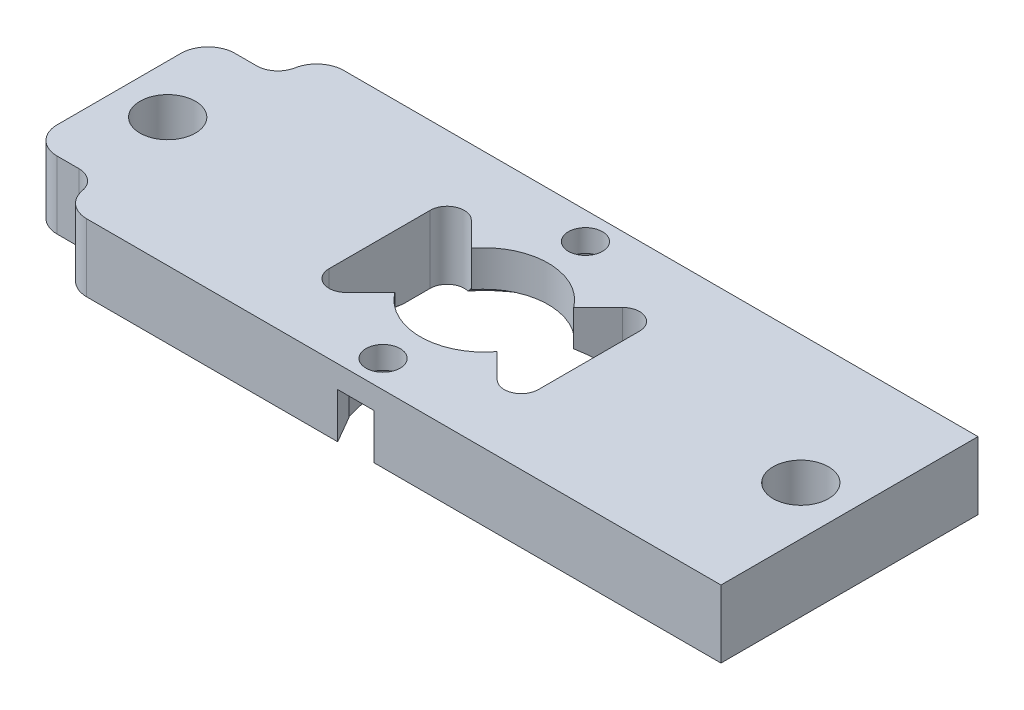
SolidWorks part; units mm, degrees
ref_plane "Front Plane" through (0, 0, 0) normal (0, 0, 1) x (1, 0, 0)
ref_plane "Top Plane" through (0, 0, 0) normal (0, 1, 0) x (1, 0, 0)
ref_plane "Right Plane" through (0, 0, 0) normal (1, 0, 0) x (0, 0, -1)
sketch "Sketch2" plane through (0, 0, 0) normal (0, 1, 0) x (1, 0, 0)
  line L1 (0, 0) -> (68.58, 0)
  line L2 (0, 0) -> (0, 24.13)
  line L3 (0, 24.13) -> (68.58, 24.13)
  line L4 (68.58, 0) -> (68.58, 24.13)
  circle A0 centre (4.57, 12.065) radius 2.6
  circle A1 centre (64.01, 12.065) radius 2.6
  point P10 (68.58, 12.065)
  dimension "D4" = 5.2
  dimension "D1" = 68.58
  dimension "D2" = 24.13
  dimension "D3" = 4.57
  dimension "D5" = 4.57
extrude "Boss-Extrude1" add sketch "Sketch2" along normal blind 6.35
sketch "Sketch3" plane through (0, 6.35, 0) normal (0, 1, 0) x (1, 0, 0)
  line L0 (6.57, 22.415) -> (6.57, 24.13)
  line L2 (4.57, 20.415) -> (0, 20.415)
  line L3 (0, 24.13) -> (0, 0) construction
  line L4 (68.58, 24.13) -> (0, 24.13) construction
  line L5 (4.57, 12.065) -> (64.01, 12.065) construction
  line L6 (34.29, 24.13) -> (34.29, 0) construction
  line L7 (0, 0) -> (68.58, 0) construction
  line L8 (6.57, 1.715) -> (6.57, 0)
  line L9 (4.57, 3.715) -> (0, 3.715)
  arc A0 (4.57, 20.415) -> (6.57, 22.415) centre (4.57, 22.415) ccw
  circle A1 centre (4.57, 12.065) radius 2.6 construction
  circle A2 centre (4.57, 12.065) radius 2.6
  arc A3 (4.57, 3.715) -> (6.57, 1.715) centre (4.57, 1.715) cw
  line M1 (0, 0) -> (68.58, 0)
  line M5 (68.58, 24.13) -> (0, 24.13)
  line M7 (0, 24.13) -> (0, 0)
  dimension "D1" = 10.35
  dimension "D2" = 4
extrude "Cut-Extrude1" cut sketch "Sketch3" against normal through all contours A3 L9 L8 M7 M1 | L2 A0 L0 M5 M7
fillet "Fillet3" radius 2.54 4 edges at (6.57, 3.175, 0) (0, 3.175, -3.715) (0, 3.175, -20.415) (6.57, 3.175, -24.13)
sketch "Sketch4" plane through (0, 6.35, 0) normal (0, 1, 0) x (1, 0, 0)
  line L0 (4.57, 12.065) -> (64.01, 12.065) construction
  circle A0 centre (34.29, 12.065) radius 6
  circle A1 centre (4.57, 12.065) radius 2.6 construction
  circle A2 centre (64.01, 12.065) radius 2.6 construction
  circle A3 centre (64.01, 12.065) radius 2.6 construction
  circle A4 centre (4.57, 12.065) radius 2.6 construction
  point P8 (34.29, 12.065)
  dimension "D1" = 12
extrude "Cut-Extrude2" cut sketch "Sketch4" against normal through all
ref_plane "Plane2" through (34.29, 0, 0) normal (1, 0, 0) x (0, 0, -1)
sketch "Sketch8" plane through (34.29, 0, 0) normal (1, 0, 0) x (0, 0, -1)
  line L0 (0, 6.35) -> (24.13, 6.35) construction
  line L1 (0, 6.35) -> (24.13, 6.35) construction
  line L2 (12.065, 6.35) -> (12.065, 0) construction
  line L3 (0, 0) -> (24.13, 0) construction
  line L4 (22.13, 0) -> (24.13, 0) construction
  line L5 (12.065, 4.35) -> (12.065, 0)
  line L6 (0, 0) -> (24.13, 0)
  circle A0 centre (12.065, -9.4692) radius 13.8192
  point P8 (12.065, 4.35)
  dimension "D1" = 2
  dimension "D2" = 2
revolve "Cut-Revolve6" cut sketch "Sketch8" angle 360 about L2
sketch "Sketch9" plane through (0, 6.35, 0) normal (0, 1, 0) x (1, 0, 0)
  line L0 (24.4628, 7.315) -> (24.4628, 16.815)
  line L1 (29.4838, 15.6567) -> (39.0962, 8.4733) construction
  line L2 (27.1941, 17.9464) -> (29.4838, 15.6567)
  line L3 (29.4838, 15.6567) -> (29.4838, 8.4733)
  line L4 (29.4838, 8.4733) -> (27.1941, 6.1836)
  line L5 (29.4838, 8.4733) -> (39.0962, 15.6567) construction
  line L6 (44.1172, 16.815) -> (44.1172, 7.315)
  line L8 (41.3859, 6.1836) -> (39.0962, 8.4733)
  line L9 (39.0962, 8.4733) -> (39.0962, 15.6567)
  line L10 (39.0962, 15.6567) -> (41.3859, 17.9464)
  circle A0 centre (34.29, 12.065) radius 9.5 construction
  circle A1 centre (34.29, 12.065) radius 6 construction
  arc A2 (24.4628, 7.315) -> (27.1941, 6.1836) centre (26.0628, 7.315) ccw
  circle A3 centre (34.29, 2.565) radius 1.6
  arc A4 (27.1941, 17.9464) -> (24.4628, 16.815) centre (26.0628, 16.815) ccw
  circle A5 centre (34.29, 21.565) radius 1.6
  arc A6 (44.1172, 16.815) -> (41.3859, 17.9464) centre (42.5172, 16.815) ccw
  arc A7 (41.3859, 6.1836) -> (44.1172, 7.315) centre (42.5172, 7.315) ccw
  point P4 (34.29, 12.065)
  point P19 (34.29, 12.065)
  dimension "D1" = 19
  dimension "D2" = 6
  dimension "D3" = 3.2
extrude "Cut-Extrude3" cut sketch "Sketch9" against normal through all
sketch "Sketch10" plane through (0, 0, 0) normal (0, -1, 0) x (1, 0, 0)
  line L1 (31.1146, -21.565) -> (32.7023, -24.315)
  line L2 (32.7023, -24.315) -> (35.8777, -24.315)
  line L3 (35.8777, -24.315) -> (37.4654, -21.565)
  line L4 (37.4654, -21.565) -> (35.8777, -18.815)
  line L5 (35.8777, -18.815) -> (32.7023, -18.815)
  line L6 (32.7023, -18.815) -> (31.1146, -21.565)
  line L7 (68.58, -24.13) -> (9.0344, -24.13) construction
  line L8 (9.0344, 0) -> (68.58, 0) construction
  line L9 (32.7023, -5.315) -> (35.8777, -5.315)
  line L10 (35.8777, -5.315) -> (37.4654, -2.565)
  line L11 (37.4654, -2.565) -> (35.8777, 0.185)
  line L12 (35.8777, 0.185) -> (32.7023, 0.185)
  line L13 (32.7023, 0.185) -> (31.1146, -2.565)
  line L14 (31.1146, -2.565) -> (32.7023, -5.315)
  circle A0 centre (34.29, -21.565) radius 2.75 construction
  arc A1 (32.7537, -22.0121) -> (35.8263, -22.0121) centre (34.29, -21.565) ccw construction
  circle A2 centre (34.29, -2.565) radius 2.75 construction
  arc A3 (35.8263, -2.1179) -> (32.7537, -2.1179) centre (34.29, -2.565) ccw construction
  dimension "D1" = 5.5
  dimension "D2" = 5.5
extrude "Cut-Extrude4" cut sketch "Sketch10" against normal blind 4.25
